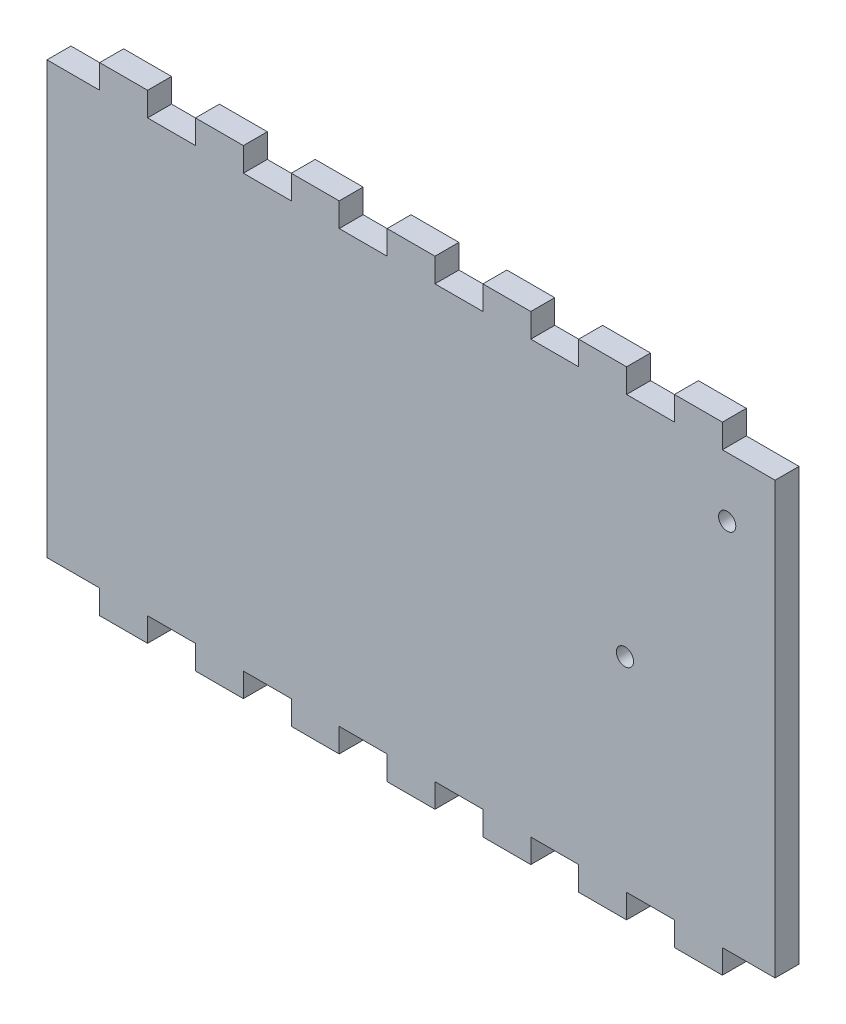
SolidWorks part; units mm, degrees
ref_plane "Front Plane" through (0, 0, 0) normal (0, 0, 1) x (1, 0, 0)
ref_plane "Top Plane" through (0, 0, 0) normal (0, 1, 0) x (1, 0, 0)
ref_plane "Right Plane" through (0, 0, 0) normal (1, 0, 0) x (0, 0, -1)
sketch "Sketch1" plane through (0, 0, 0) normal (0, 0, 1) x (1, 0, 0)
  line L1 (-48.26, 31.75) -> (48.26, 31.75)
  line L2 (-48.26, 31.75) -> (-48.26, -31.75)
  line L3 (-48.26, -31.75) -> (48.26, -31.75)
  line L4 (48.26, 31.75) -> (48.26, -31.75)
  line L5 (-48.26, 31.75) -> (48.26, -31.75) construction
  line L6 (-48.26, -31.75) -> (48.26, 31.75) construction
  point P0 (0, 0)
  dimension "D1" = 96.52
  dimension "D2" = 63.5
extrude "Boss-Extrude1" add sketch "Sketch1" along normal blind 3.175
sketch "Sketch2" plane through (0, 0, 3.175) normal (0, 0, 1) x (1, 0, 0)
  line L0 (-41.275, -28.575) -> (-48.26, -28.575)
  line L1 (-48.26, -28.575) -> (-48.26, -31.75)
  line L2 (-48.26, 31.75) -> (-48.26, -31.75) construction
  line L3 (-48.26, -31.75) -> (-41.275, -31.75)
  line L4 (-48.26, -31.75) -> (48.26, -31.75) construction
  line L5 (-41.275, -31.75) -> (-41.275, -28.575)
  line L6 (-34.925, -28.575) -> (-34.925, -31.75)
  line L7 (-34.925, -31.75) -> (-28.575, -31.75)
  line L8 (-28.575, -31.75) -> (-28.575, -28.575)
  line L9 (-28.575, -28.575) -> (-34.925, -28.575)
  line L10 (-22.225, -31.75) -> (-15.875, -31.75)
  line L11 (-15.875, -31.75) -> (-15.875, -28.575)
  line L12 (-15.875, -28.575) -> (-22.225, -28.575)
  line L13 (-22.225, -28.575) -> (-22.225, -31.75)
  line L14 (-9.525, -31.75) -> (-3.175, -31.75)
  line L15 (-3.175, -31.75) -> (-3.175, -28.575)
  line L16 (-3.175, -28.575) -> (-9.525, -28.575)
  line L17 (-9.525, -28.575) -> (-9.525, -31.75)
  line L18 (9.525, -31.75) -> (9.525, -28.575)
  line L19 (9.525, -28.575) -> (3.175, -28.575)
  line L20 (3.175, -28.575) -> (3.175, -31.75)
  line L21 (3.175, -31.75) -> (9.525, -31.75)
  line L22 (15.875, -31.75) -> (15.875, -28.575)
  line L23 (15.875, -28.575) -> (22.225, -28.575)
  line L24 (15.875, -31.75) -> (22.225, -31.75)
  line L25 (22.225, -31.75) -> (22.225, -28.575)
  line L26 (28.575, -31.75) -> (28.575, -28.575)
  line L27 (28.575, -28.575) -> (34.925, -28.575)
  line L28 (34.925, -28.575) -> (34.925, -31.75)
  line L29 (34.925, -31.75) -> (28.575, -31.75)
  line L30 (48.26, -28.575) -> (41.275, -28.575)
  line L31 (48.26, -31.75) -> (48.26, 31.75) construction
  line L32 (41.275, -28.575) -> (41.275, -31.75)
  line L33 (41.275, -31.75) -> (48.26, -31.75)
  line L34 (48.26, -31.75) -> (48.26, -28.575)
  line L35 (-48.26, 0) -> (48.26, 0) construction
  line L36 (48.26, 31.75) -> (48.26, 28.575)
  line L37 (41.275, 31.75) -> (48.26, 31.75)
  line L38 (41.275, 28.575) -> (41.275, 31.75)
  line L39 (48.26, 28.575) -> (41.275, 28.575)
  line L40 (34.925, 31.75) -> (28.575, 31.75)
  line L41 (34.925, 28.575) -> (34.925, 31.75)
  line L42 (28.575, 28.575) -> (34.925, 28.575)
  line L43 (28.575, 31.75) -> (28.575, 28.575)
  line L44 (22.225, 31.75) -> (22.225, 28.575)
  line L45 (15.875, 31.75) -> (22.225, 31.75)
  line L46 (15.875, 28.575) -> (22.225, 28.575)
  line L47 (15.875, 31.75) -> (15.875, 28.575)
  line L48 (3.175, 31.75) -> (9.525, 31.75)
  line L49 (3.175, 28.575) -> (3.175, 31.75)
  line L50 (9.525, 28.575) -> (3.175, 28.575)
  line L51 (9.525, 31.75) -> (9.525, 28.575)
  line L52 (-9.525, 28.575) -> (-9.525, 31.75)
  line L53 (-3.175, 28.575) -> (-9.525, 28.575)
  line L54 (-3.175, 31.75) -> (-3.175, 28.575)
  line L55 (-9.525, 31.75) -> (-3.175, 31.75)
  line L56 (-22.225, 28.575) -> (-22.225, 31.75)
  line L57 (-15.875, 28.575) -> (-22.225, 28.575)
  line L58 (-15.875, 31.75) -> (-15.875, 28.575)
  line L59 (-22.225, 31.75) -> (-15.875, 31.75)
  line L60 (-28.575, 28.575) -> (-34.925, 28.575)
  line L61 (-28.575, 31.75) -> (-28.575, 28.575)
  line L62 (-34.925, 31.75) -> (-28.575, 31.75)
  line L63 (-34.925, 28.575) -> (-34.925, 31.75)
  line L64 (-41.275, 31.75) -> (-41.275, 28.575)
  line L65 (-48.26, 31.75) -> (-41.275, 31.75)
  line L66 (-48.26, 28.575) -> (-48.26, 31.75)
  line L67 (-41.275, 28.575) -> (-48.26, 28.575)
  dimension "D1" = 6.985
  dimension "D2" = 6.35
  dimension "D3" = 6.35
  dimension "D4" = 3.175
  dimension "D5" = 6.35
  dimension "D6" = 6.35
  dimension "D7" = 6.35
  dimension "D8" = 6.35
  dimension "D9" = 6.35
  dimension "D10" = 6.35
extrude "Cut-Extrude1" cut sketch "Sketch2" against normal through all
sketch "Sketch3" plane through (0, 0, 3.175) normal (0, 0, 1) x (1, 0, 0)
  line L1 (48.26, -28.575) -> (48.26, 28.575) construction
  line L2 (41.275, 28.575) -> (48.26, 28.575) construction
  circle A1 centre (28.3591, -1.6383) radius 1.143
  circle A2 centre (41.91, 20.6883) radius 1.143
  dimension "D1" = 2.286
  dimension "D2" = 2.286
  dimension "D3" = 14.6939
  dimension "D4" = 22.3266
  dimension "D5" = 7.8867
  dimension "D6" = 6.35
extrude "Cut-Extrude2" cut sketch "Sketch3" against normal through all
